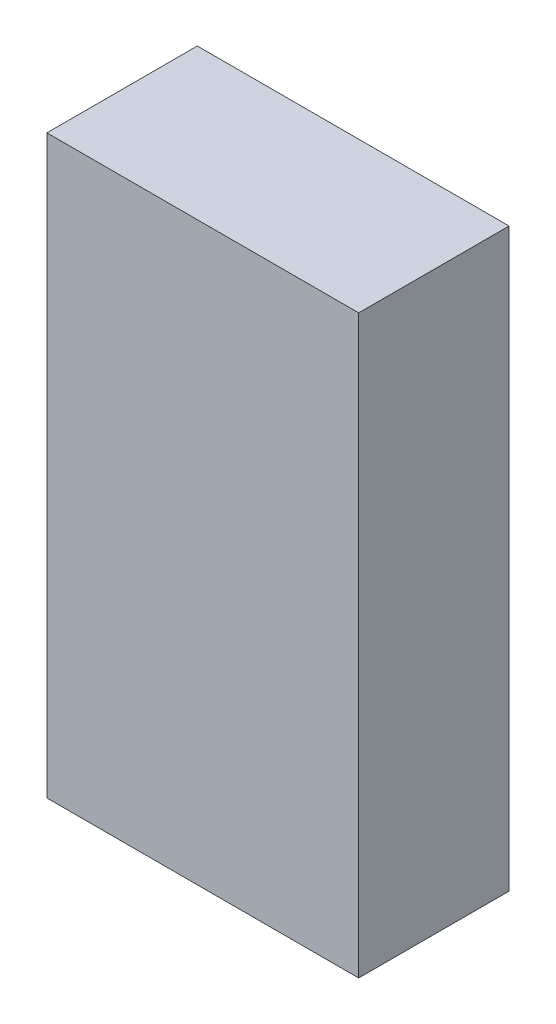
SolidWorks part; units mm, degrees
ref_plane "Front Plane" through (0, 0, 0) normal (0, 0, 1) x (1, 0, 0)
ref_plane "Top Plane" through (0, 0, 0) normal (0, 1, 0) x (1, 0, 0)
ref_plane "Right Plane" through (0, 0, 0) normal (1, 0, 0) x (0, 0, -1)
sketch "Sketch1" plane through (0, 0, 0) normal (0, 0, 1) x (1, 0, 0)
  line L0 (0, 0) -> (20.7254, 0)
  line L1 (20.7254, 0) -> (20.7254, 38.2926)
  line L2 (20.7254, 38.2926) -> (0, 38.2926)
  line L3 (0, 38.2926) -> (0, 0)
extrude "Boss-Extrude1" add sketch "Sketch1" along normal blind 10
